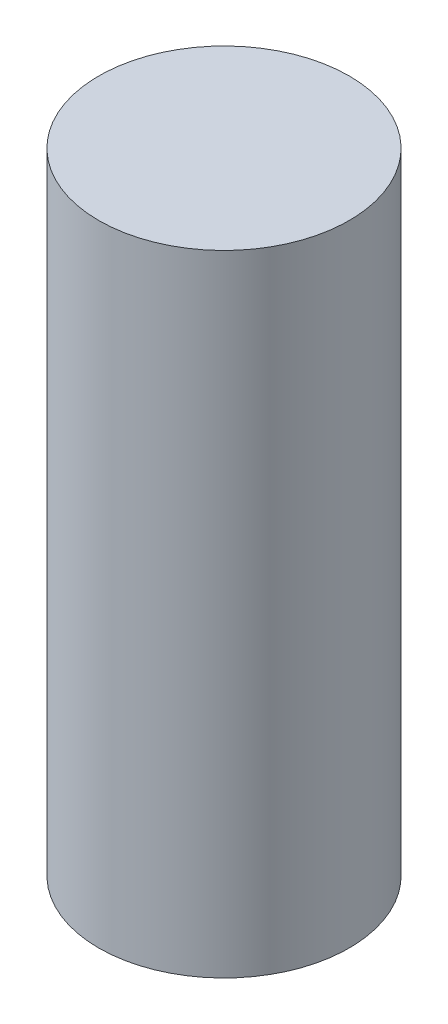
SolidWorks part; units mm, degrees
ref_plane "Front Plane" through (0, 0, 0) normal (0, 0, 1) x (1, 0, 0)
ref_plane "Top Plane" through (0, 0, 0) normal (0, 1, 0) x (1, 0, 0)
ref_plane "Right Plane" through (0, 0, 0) normal (1, 0, 0) x (0, 0, -1)
sketch "Sketch1" plane through (0, 0, 0) normal (0, 1, 0) x (1, 0, 0)
  circle A0 centre (0, 0) radius 15.9
extrude "Boss-Extrude1" add sketch "Sketch1" along normal blind 80
